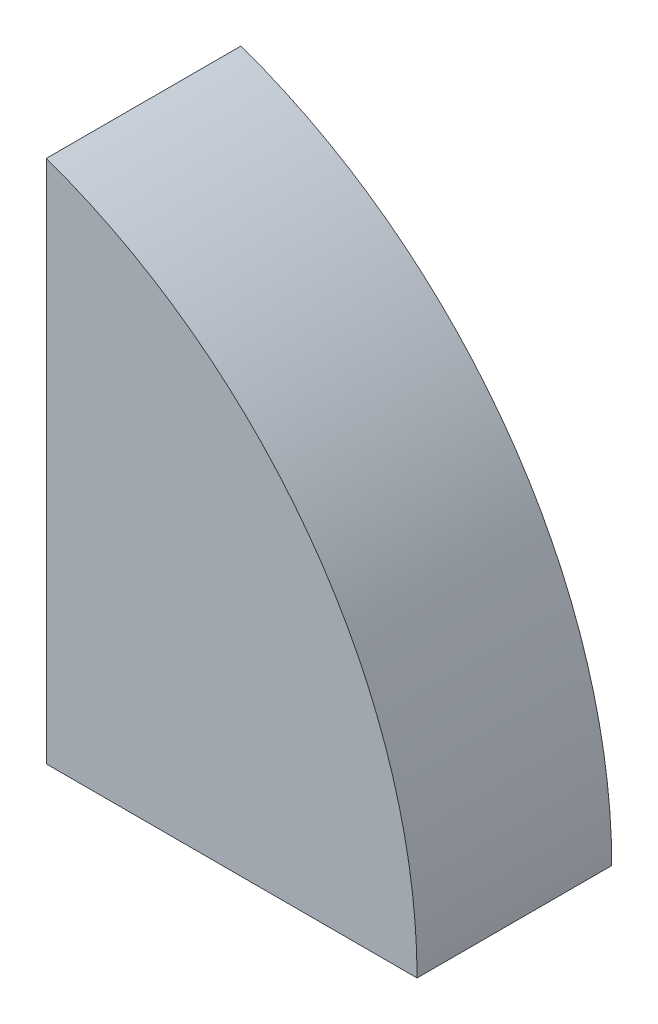
SolidWorks part; units mm, degrees
ref_plane "Plan de face" through (0, 0, 0) normal (0, 0, 1) x (1, 0, 0)
ref_plane "Plan de dessus" through (0, 0, 0) normal (0, 1, 0) x (1, 0, 0)
ref_plane "Plan de droite" through (0, 0, 0) normal (1, 0, 0) x (0, 0, -1)
sketch "Esquisse2" plane through (0, 0, 0) normal (0, 0, 1) x (1, 0, 0)
  line L0 (141.7837, -169.1228) -> (275.117, -169.1228)
  line L2 (141.7837, -169.1228) -> (141.7837, 19.439)
  arc A0 (275.117, -169.1228) -> (141.7837, 19.439) centre (75.117, -169.1228) ccw
  point P5 (141.7837, -169.1228)
  point P8 (8.4503, -169.1228)
extrude "Boss.-Extru.4" add sketch "Esquisse2" along normal blind 70
